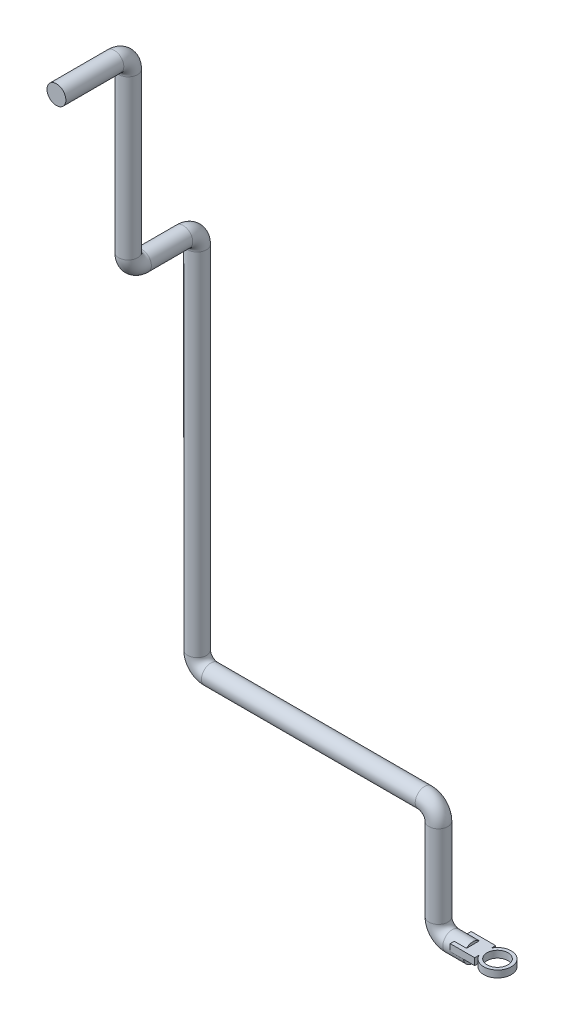
SolidWorks part; units mm, degrees
ref_plane "Alzado" through (0, 0, 0) normal (0, 0, 1) x (1, 0, 0)
ref_plane "Planta" through (0, 0, 0) normal (0, 1, 0) x (1, 0, 0)
ref_plane "Vista lateral" through (0, 0, 0) normal (1, 0, 0) x (0, 0, -1)
sketch3d "Croquis3D1"
  line L0 (0, 0, 0) -> (-30, 0, 0)
  line L1 (-50, 20, 0) -> (-50, 140, 0)
  line L2 (-70, 160, 0) -> (-380, 160, 0)
  line L3 (-400, 180, 0) -> (-400, 689.4, 0)
  line L4 (-400, 709.4, 20) -> (-400, 709.4, 80)
  line L5 (-400, 729.4, 100) -> (-400, 959.4, 100)
  line L6 (-400, 979.4, 120) -> (-400, 979.4, 204)
  arc A0 (-400, 959.4, 100) -> (-400, 979.4, 120) centre (-400, 959.4, 120) ccw
  arc A1 (-400, 709.4, 80) -> (-400, 729.4, 100) centre (-400, 729.4, 80) ccw
  arc A2 (-400, 689.4, 0) -> (-400, 709.4, 20) centre (-400, 689.4, 20) ccw
  arc A3 (-380, 160, 0) -> (-400, 180, 0) centre (-380, 180, 0) ccw
  arc A4 (-50, 140, 0) -> (-70, 160, 0) centre (-70, 140, 0) ccw
  arc A5 (-30, 0, 0) -> (-50, 20, 0) centre (-30, 20, 0) ccw
  point P12 (-400, 979.4, 100)
  point P13 (-380, 959.4, 120)
  point P16 (-400, 709.4, 100)
  point P17 (-420, 729.4, 80)
  point P20 (-400, 709.4, 0)
  point P21 (-380, 689.4, 20)
  point P24 (-400, 160, 0)
  point P25 (-380, 180, -20)
  point P28 (-50, 160, 0)
  point P29 (-70, 140, 20)
  point P32 (-50, 0, 0)
  point P33 (-30, 20, -20)
  dimension "D8" = 20
  dimension "D1" = 50
  dimension "D2" = 160
  dimension "D3" = 350
  dimension "D4" = 549.4
  dimension "D5" = 100
  dimension "D6" = 270
  dimension "D7" = 104
sketch "Croquis1" plane through (0, 0, 0) normal (1, 0, 0) x (0, 0, -1)
  circle A0 centre (0, 0) radius 13.7
  dimension "D1" = 27.4
sweep "Barrer1" add profiles "Croquis1" path "Croquis3D1"
sketch "Croquis2" plane through (0, 0, 0) normal (0, 1, 0) x (1, 0, 0)
  line L1 (17.743, -8.8561) -> (17.743, -15.2155)
  line L2 (-17.743, 15.2155) -> (17.743, 15.2155)
  line L3 (-17.743, 15.2155) -> (-17.743, -15.2155)
  line L4 (-17.743, -15.2155) -> (17.743, -15.2155)
  line L5 (17.743, 15.2155) -> (17.743, 8.8561)
  line L6 (-17.743, 15.2155) -> (17.743, -15.2155) construction
  line L7 (-17.743, -15.2155) -> (17.743, 15.2155) construction
  circle A0 centre (35.6702, 0) radius 19.9954
  circle A1 centre (35.6702, 0) radius 15.2155
extrude "Saliente-Extruir1" add sketch "Croquis2" along normal blind 10 contours A0 L5 L2 L3 L4 L1 | A0 A1
